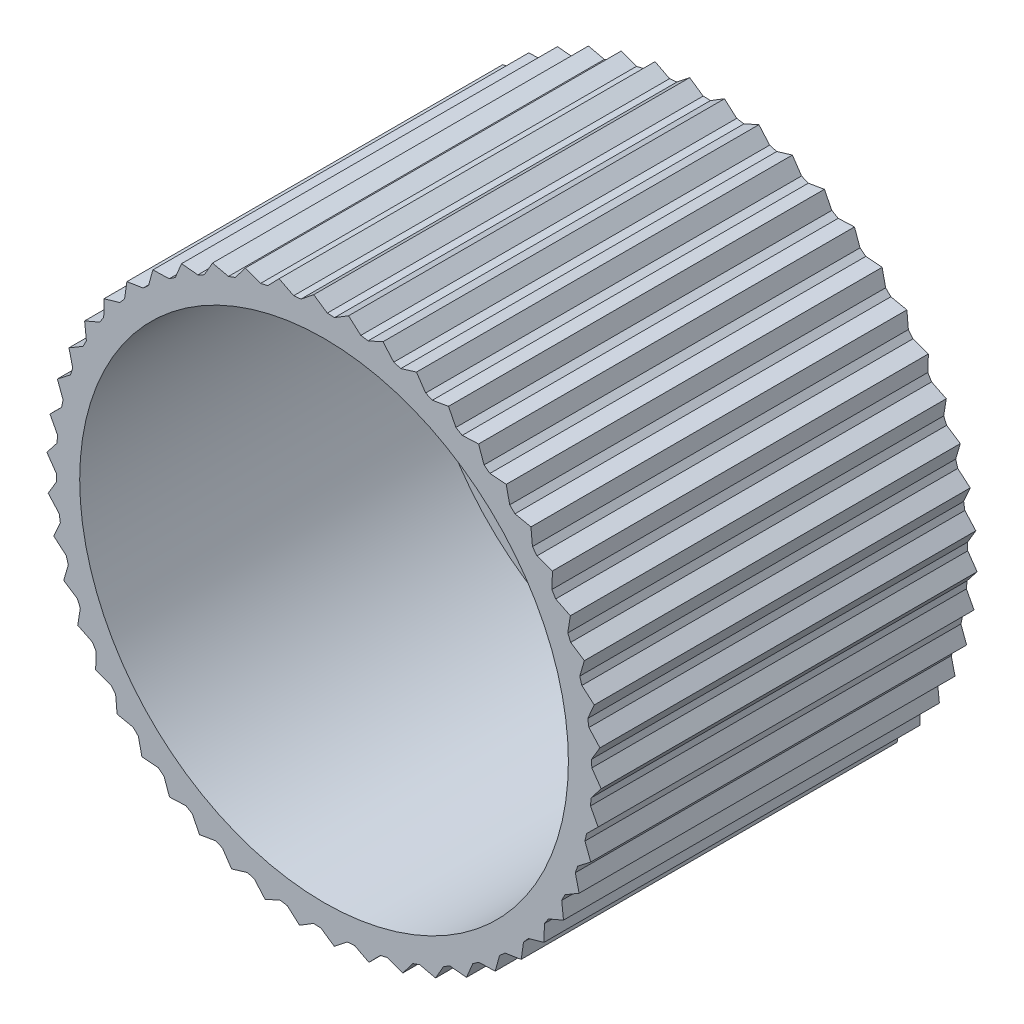
SolidWorks part; units mm, degrees
ref_plane "Plan de face" through (0, 0, 0) normal (0, 0, 1) x (1, 0, 0)
ref_plane "Plan de dessus" through (0, 0, 0) normal (0, 1, 0) x (1, 0, 0)
ref_plane "Plan de droite" through (0, 0, 0) normal (1, 0, 0) x (0, 0, -1)
sketch "Esquisse1" plane through (0, 0, 0) normal (0, 0, 1) x (1, 0, 0)
  line L0 (12.3066, -7.1841) -> (12.7384, -7.4361) construction
  line L1 (12.7384, -7.4361) -> (12.6445, -6.571)
  line L2 (12.7384, -7.4361) -> (11.9389, -7.7797)
  line L3 (11.7059, -8.974) -> (10.8697, -9.2147)
  line L4 (11.7059, -8.974) -> (11.7212, -8.104)
  line L5 (10.4889, -10.3704) -> (9.6291, -10.5044)
  line L6 (10.4889, -10.3704) -> (10.6131, -9.5092)
  line L7 (9.1064, -11.6033) -> (8.2366, -11.6284)
  line L8 (9.1064, -11.6033) -> (9.3376, -10.7644)
  line L9 (7.5803, -12.6531) -> (6.7142, -12.5691)
  line L10 (7.5803, -12.6531) -> (7.9149, -11.8498)
  line L11 (5.9347, -13.5034) -> (5.086, -13.3115)
  line L12 (5.9347, -13.5034) -> (6.3673, -12.7483)
  line L13 (4.1955, -14.1407) -> (3.3775, -13.844)
  line L14 (4.1955, -14.1407) -> (4.7193, -13.4459)
  line L15 (2.3901, -14.5551) -> (1.6158, -14.1581)
  line L16 (2.3901, -14.5551) -> (2.9968, -13.9313)
  line L17 (0.547, -14.7399) -> (-0.1715, -14.249)
  line L18 (0.547, -14.7399) -> (1.2272, -14.1971)
  line L19 (-1.3047, -14.6922) -> (-1.956, -14.1151)
  line L20 (-1.3047, -14.6922) -> (-0.5619, -14.2389)
  line L21 (-3.1358, -14.4128) -> (-3.7096, -13.7587)
  line L22 (-3.1358, -14.4128) -> (-2.3421, -14.0562)
  line L23 (-4.9175, -13.9061) -> (-5.4048, -13.1852)
  line L24 (-4.9175, -13.9061) -> (-4.0853, -13.6518)
  line L25 (-6.6216, -13.1802) -> (-7.0147, -12.4039)
  line L26 (-6.6216, -13.1802) -> (-5.7641, -13.0322)
  line L27 (-8.2213, -12.2463) -> (-8.514, -11.4269)
  line L28 (-8.2213, -12.2463) -> (-7.352, -12.207)
  line L29 (-9.6914, -11.1194) -> (-9.8791, -10.2697)
  line L30 (-9.6914, -11.1194) -> (-8.824, -11.1893)
  line L31 (-11.0086, -9.817) -> (-11.0883, -8.9505)
  line L32 (-11.0086, -9.817) -> (-10.1568, -9.9951)
  line L33 (-12.1522, -8.3599) -> (-12.1227, -7.4902)
  line L34 (-12.1522, -8.3599) -> (-11.3294, -8.6433)
  line L35 (-13.1041, -6.7709) -> (-12.9659, -5.9118)
  line L36 (-13.1041, -6.7709) -> (-12.3234, -7.1552)
  line L37 (-13.8494, -5.0751) -> (-13.6046, -4.2401)
  line L38 (-13.8494, -5.0751) -> (-13.123, -5.5542)
  line L39 (-14.3763, -3.2993) -> (-14.0287, -2.5016)
  line L40 (-14.3763, -3.2993) -> (-13.7156, -3.8657)
  line L41 (-14.6764, -1.4715) -> (-14.2316, -0.7236)
  line L42 (-14.6764, -1.4715) -> (-14.092, -2.1162)
  line L43 (-14.7451, 0.3796) -> (-14.2101, 1.0658)
  line L44 (-14.7451, 0.3796) -> (-14.2461, -0.3333)
  line L45 (-14.5813, 2.2246) -> (-13.9645, 2.8384)
  line L46 (-14.5813, 2.2246) -> (-14.1755, 1.4548)
  line L47 (-14.1875, 4.0346) -> (-13.4986, 4.5662)
  line L48 (-14.1875, 4.0346) -> (-13.8814, 3.22)
  line L49 (-13.5699, 5.781) -> (-12.8199, 6.2221)
  line L50 (-13.5699, 5.781) -> (-13.3684, 4.9344)
  line L51 (-12.7384, 7.4361) -> (-11.9389, 7.7797)
  line L52 (-12.7384, 7.4361) -> (-12.6445, 6.571)
  line L53 (-11.7059, 8.974) -> (-10.8697, 9.2147)
  line L54 (-11.7059, 8.974) -> (-11.7212, 8.104)
  line L55 (-10.4889, 10.3704) -> (-9.6291, 10.5044)
  line L56 (-10.4889, 10.3704) -> (-10.6131, 9.5092)
  line L57 (-9.1064, 11.6033) -> (-8.2366, 11.6284)
  line L58 (-9.1064, 11.6033) -> (-9.3376, 10.7644)
  line L59 (-7.5803, 12.6531) -> (-6.7142, 12.5691)
  line L60 (-7.5803, 12.6531) -> (-7.9149, 11.8498)
  line L61 (-5.9347, 13.5034) -> (-5.086, 13.3115)
  line L62 (-5.9347, 13.5034) -> (-6.3673, 12.7483)
  line L63 (-4.1955, 14.1407) -> (-3.3775, 13.844)
  line L64 (-4.1955, 14.1407) -> (-4.7193, 13.4459)
  line L65 (-2.3901, 14.5551) -> (-1.6158, 14.1581)
  line L66 (-2.3901, 14.5551) -> (-2.9968, 13.9313)
  line L67 (-0.547, 14.7399) -> (0.1715, 14.249)
  line L68 (-0.547, 14.7399) -> (-1.2272, 14.1971)
  line L69 (1.3047, 14.6922) -> (1.956, 14.1151)
  line L70 (1.3047, 14.6922) -> (0.5619, 14.2389)
  line L71 (3.1358, 14.4128) -> (3.7096, 13.7587)
  line L72 (3.1358, 14.4128) -> (2.3421, 14.0562)
  line L73 (4.9175, 13.9061) -> (5.4048, 13.1852)
  line L74 (4.9175, 13.9061) -> (4.0853, 13.6518)
  line L75 (6.6216, 13.1802) -> (7.0147, 12.4039)
  line L76 (6.6216, 13.1802) -> (5.7641, 13.0322)
  line L77 (8.2213, 12.2463) -> (8.514, 11.4269)
  line L78 (8.2213, 12.2463) -> (7.352, 12.207)
  line L79 (9.6914, 11.1194) -> (9.8791, 10.2697)
  line L80 (9.6914, 11.1194) -> (8.824, 11.1893)
  line L81 (11.0086, 9.817) -> (11.0883, 8.9505)
  line L82 (11.0086, 9.817) -> (10.1568, 9.9951)
  line L83 (12.1522, 8.3599) -> (12.1227, 7.4902)
  line L84 (12.1522, 8.3599) -> (11.3294, 8.6433)
  line L85 (13.1041, 6.7709) -> (12.9659, 5.9118)
  line L86 (13.1041, 6.7709) -> (12.3234, 7.1552)
  line L87 (13.8494, 5.0751) -> (13.6046, 4.2401)
  line L88 (13.8494, 5.0751) -> (13.123, 5.5542)
  line L89 (14.3763, 3.2993) -> (14.0287, 2.5016)
  line L90 (14.3763, 3.2993) -> (13.7156, 3.8657)
  line L91 (14.6764, 1.4715) -> (14.2316, 0.7236)
  line L92 (14.6764, 1.4715) -> (14.092, 2.1162)
  line L93 (14.7451, -0.3796) -> (14.2101, -1.0658)
  line L94 (14.7451, -0.3796) -> (14.2461, 0.3333)
  line L95 (14.5813, -2.2246) -> (13.9645, -2.8384)
  line L96 (14.5813, -2.2246) -> (14.1755, -1.4548)
  line L97 (14.1875, -4.0346) -> (13.4986, -4.5662)
  line L98 (14.1875, -4.0346) -> (13.8814, -3.22)
  line L99 (13.5699, -5.781) -> (12.8199, -6.2221)
  line L100 (13.5699, -5.781) -> (13.3684, -4.9344)
  line L201 (11.9389, -7.7797) -> (11.7212, -8.104)
  line L202 (10.8697, -9.2147) -> (10.6131, -9.5092)
  line L203 (9.6291, -10.5044) -> (9.3376, -10.7644)
  line L204 (8.2366, -11.6284) -> (7.9149, -11.8498)
  line L205 (6.7142, -12.5691) -> (6.3673, -12.7483)
  line L206 (5.086, -13.3115) -> (4.7193, -13.4459)
  line L207 (3.3775, -13.844) -> (2.9968, -13.9313)
  line L208 (1.6158, -14.1581) -> (1.2272, -14.1971)
  line L209 (-0.1715, -14.249) -> (-0.5619, -14.2389)
  line L210 (-1.956, -14.1151) -> (-2.3421, -14.0562)
  line L211 (-3.7096, -13.7587) -> (-4.0853, -13.6518)
  line L212 (-5.4048, -13.1852) -> (-5.7641, -13.0322)
  line L213 (-7.0147, -12.4039) -> (-7.352, -12.207)
  line L214 (-8.514, -11.4269) -> (-8.824, -11.1893)
  line L215 (-9.8791, -10.2697) -> (-10.1568, -9.9951)
  line L216 (-11.0883, -8.9505) -> (-11.3294, -8.6433)
  line L217 (-12.1227, -7.4902) -> (-12.3234, -7.1552)
  line L218 (-12.9659, -5.9118) -> (-13.123, -5.5542)
  line L219 (-13.6046, -4.2401) -> (-13.7156, -3.8657)
  line L220 (-14.0287, -2.5016) -> (-14.092, -2.1162)
  line L221 (-14.2316, -0.7236) -> (-14.2461, -0.3333)
  line L222 (-14.2101, 1.0658) -> (-14.1755, 1.4548)
  line L223 (-13.9645, 2.8384) -> (-13.8814, 3.22)
  line L224 (-13.4986, 4.5662) -> (-13.3684, 4.9344)
  line L225 (-12.8199, 6.2221) -> (-12.6445, 6.571)
  line L226 (-11.9389, 7.7797) -> (-11.7212, 8.104)
  line L227 (-10.8697, 9.2147) -> (-10.6131, 9.5092)
  line L228 (-9.6291, 10.5044) -> (-9.3376, 10.7644)
  line L229 (-8.2366, 11.6284) -> (-7.9149, 11.8498)
  line L230 (-6.7142, 12.5691) -> (-6.3673, 12.7483)
  line L231 (-5.086, 13.3115) -> (-4.7193, 13.4459)
  line L232 (-3.3775, 13.844) -> (-2.9968, 13.9313)
  line L233 (-1.6158, 14.1581) -> (-1.2272, 14.1971)
  line L234 (0.1715, 14.249) -> (0.5619, 14.2389)
  line L235 (1.956, 14.1151) -> (2.3421, 14.0562)
  line L236 (3.7096, 13.7587) -> (4.0853, 13.6518)
  line L237 (5.4048, 13.1852) -> (5.7641, 13.0322)
  line L238 (7.0147, 12.4039) -> (7.352, 12.207)
  line L239 (8.514, 11.4269) -> (8.824, 11.1893)
  line L240 (9.8791, 10.2697) -> (10.1568, 9.9951)
  line L241 (11.0883, 8.9505) -> (11.3294, 8.6433)
  line L242 (12.1227, 7.4902) -> (12.3234, 7.1552)
  line L243 (12.9659, 5.9118) -> (13.123, 5.5542)
  line L244 (13.6046, 4.2401) -> (13.7156, 3.8657)
  line L245 (14.0287, 2.5016) -> (14.092, 2.1162)
  line L246 (14.2316, 0.7236) -> (14.2461, 0.3333)
  line L247 (14.2101, -1.0658) -> (14.1755, -1.4548)
  line L248 (13.9645, -2.8384) -> (13.8814, -3.22)
  line L249 (13.4986, -4.5662) -> (13.3684, -4.9344)
  line L250 (12.8199, -6.2221) -> (12.6445, -6.571)
  circle A0 centre (0, 0) radius 14.75 construction
  circle A1 centre (0, 0) radius 1
  circle A2 centre (0, 0) radius 14.25 construction
  point P309 (0, 0)
  dimension "D1" = 29.5
  dimension "D2" = 2
  dimension "D3" = 28.5
  dimension "D4" = 0.7
  dimension "D5" = 50
extrude "Boss.-Extru.1" add sketch "Esquisse1" along normal blind 20
sketch "Esquisse2" plane through (0, 0, 20) normal (0, 0, 1) x (1, 0, 0)
  circle A0 centre (0, 0) radius 13
  circle A1 centre (0, 0) radius 3
  dimension "D1" = 6
  dimension "D2" = 26
extrude "Enlèv. mat.-Extru.1" cut sketch "Esquisse2" against normal blind 18
sketch "Esquisse3" plane through (0, 0, 20) normal (0, 0, 1) x (1, 0, 0)
  circle A0 centre (0, 0) radius 3
  dimension "D1" = 6
extrude "Enlèv. mat.-Extru.2" cut sketch "Esquisse3" against normal blind 15
